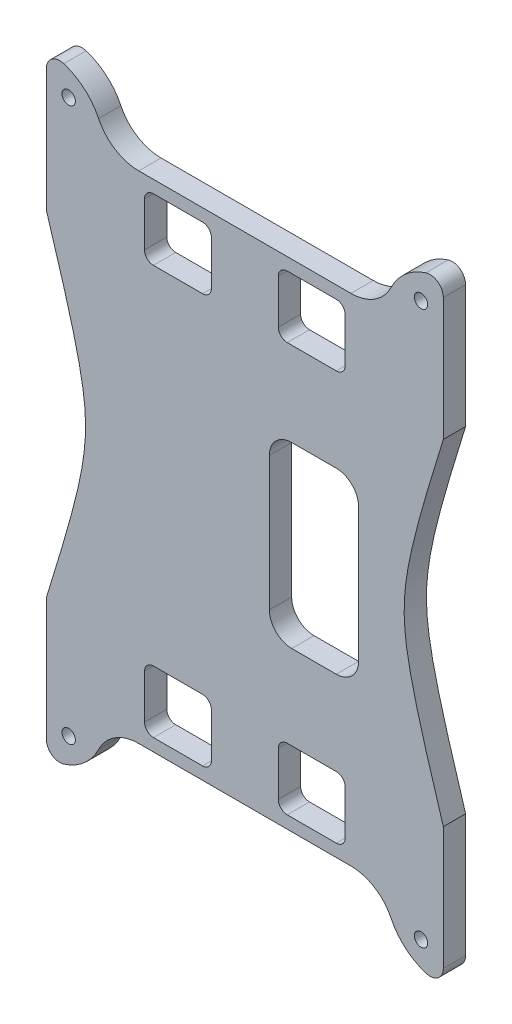
SolidWorks part; units mm, degrees
material "Acrílico (médio-alto impacto)"
ref_plane "Plano frontal" through (0, 0, 0) normal (0, 0, 1) x (1, 0, 0)
ref_plane "Plano superior" through (0, 0, 0) normal (0, 1, 0) x (1, 0, 0)
ref_plane "Plano direito" through (0, 0, 0) normal (1, 0, 0) x (0, 0, -1)
sketch "Esboço1" plane through (0, 0, 0) normal (0, 0, 1) x (1, 0, 0)
  line L0 (-8.0639, -17.8011) -> (-8.0639, -38.9203) construction
  line L1 (-31.8516, -17.8011) -> (-27.0639, -17.8011)
  line L2 (36.4361, 0.1989) -> (36.4361, -17.8011)
  line L3 (15.7238, -17.8011) -> (10.9361, -17.8011)
  line L4 (36.4361, -27.3405) -> (36.4361, -17.8011)
  line L5 (-52.5639, -27.3405) -> (-52.5639, -17.8011)
  line L6 (-52.5639, 0.1989) -> (-52.5639, -17.8011)
  line L7 (10.9361, -17.8011) -> (-27.0639, -17.8011) construction
  line L10 (36.4361, 37.7989) -> (10.9361, 37.7989) construction
  line L11 (10.9361, 93.3989) -> (-27.0639, 93.3989) construction
  line L12 (-8.0639, 93.3989) -> (-8.0639, 114.5181) construction
  line L13 (10.9361, 93.3989) -> (-27.0639, 93.3989)
  line L14 (-52.5639, 75.3989) -> (-52.5639, 93.3989)
  line L15 (-52.5639, 102.9383) -> (-52.5639, 93.3989)
  line L16 (36.4361, 102.9383) -> (36.4361, 93.3989)
  line L17 (10.9361, -17.8011) -> (-27.0639, -17.8011)
  line L18 (15.7238, 93.3989) -> (10.9361, 93.3989)
  line L19 (36.4361, 75.3989) -> (36.4361, 93.3989)
  line L20 (-31.8516, 93.3989) -> (-27.0639, 93.3989)
  arc A0 (24.7292, -23.4533) -> (32.5361, -30.2023) centre (36.4361, -17.8011) ccw
  arc A1 (24.7292, -23.4533) -> (15.7238, -17.8011) centre (15.7238, -27.8011) ccw
  arc A2 (-52.5639, -27.3405) -> (-48.6639, -30.2023) centre (-49.5639, -27.3405) ccw
  arc A3 (-40.8569, -23.4533) -> (-31.8516, -17.8011) centre (-31.8516, -27.8011) cw
  arc A4 (-40.8569, -23.4533) -> (-48.6639, -30.2023) centre (-52.5639, -17.8011) cw
  arc A5 (36.4361, -27.3405) -> (32.5361, -30.2023) centre (33.4361, -27.3405) cw
  arc A6 (36.4361, 102.9383) -> (32.5361, 105.8001) centre (33.4361, 102.9383) ccw
  arc A7 (-40.8569, 99.0511) -> (-48.6639, 105.8001) centre (-52.5639, 93.3989) ccw
  arc A8 (-40.8569, 99.0511) -> (-31.8516, 93.3989) centre (-31.8516, 103.3989) ccw
  arc A9 (-52.5639, 102.9383) -> (-48.6639, 105.8001) centre (-49.5639, 102.9383) cw
  arc A10 (24.7292, 99.0511) -> (15.7238, 93.3989) centre (15.7238, 103.3989) cw
  arc A11 (24.7292, 99.0511) -> (32.5361, 105.8001) centre (36.4361, 93.3989) cw
  conic Q0 (36.4361, 75.3989) -> (36.4361, 0.1989) control (24.7292, 37.7989) rho 0.75
  conic Q1 (-52.5639, 75.3989) -> (-52.5639, 0.1989) control (-40.8569, 37.7989) rho 0.75
  point P14 (-52.5639, -30.8011)
  point P21 (36.4361, -30.8011)
  point P45 (36.4361, 106.3989)
  point P46 (-52.5639, 106.3989)
  dimension "D1" = 26
  dimension "D2" = 20
  dimension "D8" = 13
  dimension "D9" = 3
  dimension "D11" = 10
  dimension "D3" = 25.5
  dimension "D4" = 18
  dimension "D6" = 75.2
  dimension "D10" = 9.5394
extrude "Ressalto-extrusão3" add sketch "Esboço1" along normal blind 5
sketch "Esboço4" plane through (0, 0, 0) normal (0, 0, -1) x (-1, 0, 0)
  line L0 (-36.4361, 75.3989) -> (-36.4361, 102.9383) construction
  line L1 (52.5639, 102.9383) -> (52.5639, 75.3989) construction
  line L2 (-15.7238, 93.3989) -> (31.8516, 93.3989) construction
  line L3 (-44.641, 37.7989) -> (77.6477, 37.7989) construction
  line L4 (-12.4361, 90.5989) -> (-1.4361, 90.5989)
  line L5 (-14.4361, 88.5989) -> (-14.4361, 78.6989)
  line L6 (-12.4361, 76.6989) -> (-1.4361, 76.6989)
  line L7 (0.5639, 88.5989) -> (0.5639, 78.6989)
  line L8 (17.5639, 90.5989) -> (28.5639, 90.5989)
  line L9 (15.5639, 88.5989) -> (15.5639, 78.6989)
  line L10 (17.5639, 76.6989) -> (28.5639, 76.6989)
  line L11 (30.5639, 88.5989) -> (30.5639, 78.6989)
  line L12 (-36.4361, -27.3405) -> (-36.4361, 0.1989) construction
  line L14 (31.8516, -17.8011) -> (-15.7238, -17.8011) construction
  line L15 (30.5639, -13.0011) -> (30.5639, -3.1011)
  line L16 (17.5639, -1.1011) -> (28.5639, -1.1011)
  line L17 (15.5639, -13.0011) -> (15.5639, -3.1011)
  line L18 (17.5639, -15.0011) -> (28.5639, -15.0011)
  line L19 (0.5639, -13.0011) -> (0.5639, -3.1011)
  line L20 (-12.4361, -1.1011) -> (-1.4361, -1.1011)
  line L21 (-14.4361, -13.0011) -> (-14.4361, -3.1011)
  line L22 (-12.4361, -15.0011) -> (-1.4361, -15.0011)
  circle A0 centre (-31.4361, 99.8001) radius 1.5
  circle A1 centre (47.5639, 99.8001) radius 1.5
  arc A3 (28.5639, 76.6989) -> (30.5639, 78.6989) centre (28.5639, 78.6989) ccw
  arc A4 (28.5639, 90.5989) -> (30.5639, 88.5989) centre (28.5639, 88.5989) cw
  arc A5 (17.5639, 90.5989) -> (15.5639, 88.5989) centre (17.5639, 88.5989) ccw
  arc A6 (15.5639, 78.6989) -> (17.5639, 76.6989) centre (17.5639, 78.6989) ccw
  arc A7 (-1.4361, 76.6989) -> (0.5639, 78.6989) centre (-1.4361, 78.6989) ccw
  arc A8 (-1.4361, 90.5989) -> (0.5639, 88.5989) centre (-1.4361, 88.5989) cw
  arc A9 (-12.4361, 90.5989) -> (-14.4361, 88.5989) centre (-12.4361, 88.5989) ccw
  arc A10 (-14.4361, 78.6989) -> (-12.4361, 76.6989) centre (-12.4361, 78.6989) ccw
  arc A11 (-14.4361, -3.1011) -> (-12.4361, -1.1011) centre (-12.4361, -3.1011) cw
  arc A12 (-12.4361, -15.0011) -> (-14.4361, -13.0011) centre (-12.4361, -13.0011) cw
  arc A13 (-1.4361, -15.0011) -> (0.5639, -13.0011) centre (-1.4361, -13.0011) ccw
  arc A14 (-1.4361, -1.1011) -> (0.5639, -3.1011) centre (-1.4361, -3.1011) cw
  arc A15 (15.5639, -3.1011) -> (17.5639, -1.1011) centre (17.5639, -3.1011) cw
  arc A16 (17.5639, -15.0011) -> (15.5639, -13.0011) centre (17.5639, -13.0011) cw
  arc A17 (28.5639, -15.0011) -> (30.5639, -13.0011) centre (28.5639, -13.0011) ccw
  arc A18 (28.5639, -1.1011) -> (30.5639, -3.1011) centre (28.5639, -3.1011) cw
  circle A20 centre (47.5639, -24.2023) radius 1.5
  circle A21 centre (-31.4361, -24.2023) radius 1.5
  point P24 (30.5639, 76.6989)
  point P31 (15.5639, 76.6989)
  point P34 (0.5639, 76.6989)
  point P41 (-14.4361, 76.6989)
  point P46 (16.5034, 37.7989)
  point P79 (-14.4361, -1.1011)
  point P80 (0.5639, -1.1011)
  point P81 (15.5639, -1.1011)
  point P82 (30.5639, -1.1011)
  dimension "D1" = 3
  dimension "D3" = 3
  dimension "D4" = 5
  dimension "D5" = 6
  dimension "D6" = 5
  dimension "D7" = 6
  dimension "D16" = 2
  dimension "D10" = 52
  dimension "D11" = 52
  dimension "D12" = 2.8
  dimension "D13" = 2.8
  dimension "D14" = 15
  dimension "D15" = 15
  dimension "D17" = 90
  dimension "D18" = 55.6
extrude "Corte-extrusão3" cut sketch "Esboço4" against normal blind 10
sketch "Esboço5" plane through (0, 0, 5) normal (0, 0, 1) x (1, 0, 0)
  line L1 (2.4361, 17.7989) -> (12.4361, 17.7989)
  line L2 (-2.5639, 22.7989) -> (-2.5639, 52.7989)
  line L3 (2.4361, 57.7989) -> (12.4361, 57.7989)
  line L4 (17.4361, 22.7989) -> (17.4361, 52.7989)
  line L5 (-52.5639, 102.9383) -> (-52.5639, 75.3989) construction
  arc A0 (2.4361, 17.7989) -> (-2.5639, 22.7989) centre (2.4361, 22.7989) cw
  arc A1 (12.4361, 17.7989) -> (17.4361, 22.7989) centre (12.4361, 22.7989) ccw
  arc A2 (12.4361, 57.7989) -> (17.4361, 52.7989) centre (12.4361, 52.7989) cw
  arc A3 (-2.5639, 52.7989) -> (2.4361, 57.7989) centre (2.4361, 52.7989) cw
  point P12 (-2.5639, 17.7989)
  point P15 (17.4361, 17.7989)
  point P18 (17.4361, 57.7989)
  dimension "D5" = 5
  dimension "D2" = 40
  dimension "D3" = 20
  dimension "D4" = 50
extrude "Corte-extrusão4" cut sketch "Esboço5" against normal blind 10
